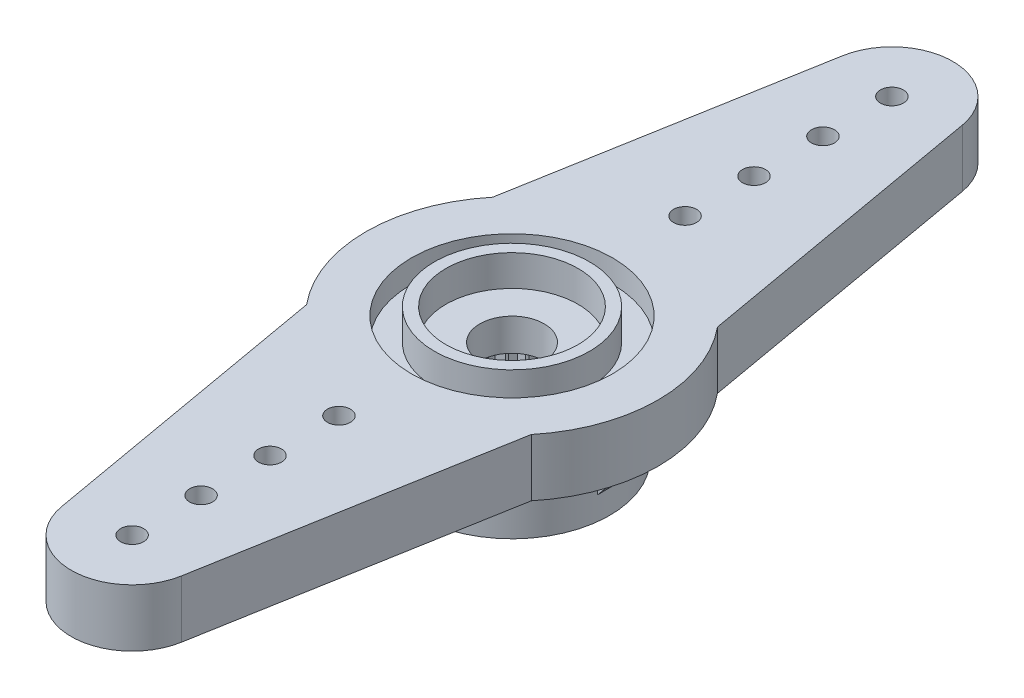
SolidWorks part; units mm, degrees
material "PC High Viscosity"
ref_plane "Front Plane" through (0, 0, 0) normal (0, 0, 1) x (1, 0, 0)
ref_plane "Top Plane" through (0, 0, 0) normal (0, 1, 0) x (1, 0, 0)
ref_plane "Right Plane" through (0, 0, 0) normal (1, 0, 0) x (0, 0, -1)
sketch "BaseS" plane through (0, 0, 0) normal (0, 1, 0) x (1, 0, 0)
  circle A0 centre (0, 0) radius 6.35
  dimension "D1" = 12.7
extrude "BASE" add sketch "BaseS" along normal blind 5.4
sketch "TopBoreS" plane through (0, 5.4, 0) normal (0, 1, 0) x (1, 0, 0)
  circle A0 centre (0, 0) radius 1.4
  dimension "D1" = 2.8
extrude "TOP BORE" cut sketch "TopBoreS" against normal through all
sketch "HornHalfS" plane through (0, 5.4, 0) normal (0, 1, 0) x (1, 0, 0)
  line L0 (0, 0) -> (0, 16.53) construction
  line L1 (-2.6097, 16.9902) -> (-4.8916, 4.049)
  line L2 (0, 19.18) -> (0, 16.53) construction
  line L3 (2.6097, 16.9902) -> (4.8916, 4.049)
  arc A0 (2.6097, 16.9902) -> (-2.6097, 16.9902) centre (0, 16.53) ccw
  arc A1 (4.8916, 4.049) -> (-4.8916, 4.049) centre (0, 0) ccw
  circle A2 centre (0, 0) radius 6.35 construction
  dimension "D1" = 5.3
  dimension "D2" = 19.18
  dimension "D3" = 10
  dimension "D4" = 9.7832
extrude "HORN HALF" add sketch "HornHalfS" against normal blind 2.5
sketch "HornAttachS" plane through (0, 5.4, 0) normal (0, 1, 0) x (1, 0, 0)
  circle A0 centre (0, 16.53) radius 0.5
  dimension "D1" = 1
extrude "HORN ATTACH" cut sketch "HornAttachS" against normal through all
sketch "HA LP RS" plane through (0, 0, 0) normal (0, 1, 0) x (1, 0, 0)
  line L0 (0, 0) -> (0, 16.53) construction
pattern_linear "HA LP" count 4 spacing 3 along (0, 0, 1) of "HORN ATTACH"
mirror "HORN BODIES" about plane through (0, 0, 0) normal (0, 0, 1) of "HA LP", "HORN ATTACH", "HORN HALF"
sketch "ToothS" plane through (0, 0, 0) normal (0, -1, 0) x (1, 0, 0)
  line L0 (0, -2.9) -> (0.2629, -2.5867)
  line L1 (0, -2.9) -> (-0.2629, -2.5867)
  line L2 (0, -2.6) -> (0, -2.9) construction
  line L3 (0, 0) -> (0, -2.6) construction
  arc A0 (-0.2629, -2.5867) -> (0.2629, -2.5867) centre (0, 0) ccw
  dimension "D1" = 5.2
  dimension "D2" = 80
  dimension "D3" = 0.3
extrude "TOOTH" cut sketch "ToothS" against normal blind 3
pattern_circular "TOOTH CP" count 26 over 360 about axis through (0, 0, 0) along (0, 1, 0) of "TOOTH"
sketch "BottomBoreS" plane through (0, 0, 0) normal (0, -1, 0) x (-1, 0, 0)
  circle A0 centre (0, 0) radius 2.6
  arc A1 (0.2629, 2.5867) -> (-0.2629, 2.5867) centre (0, 0) ccw construction
extrude "BOTTOM BORE" cut sketch "BottomBoreS" against normal up to surface (3 mm away) up to face at (-0.6451, 3, 2.6172)
sketch "HoldingShaftS" plane through (0, 0, 0) normal (0, -1, 0) x (1, 0, 0)
  circle A0 centre (0, 0) radius 6.35 construction
  circle A1 centre (0, 0) radius 6.35
  circle A2 centre (0, 0) radius 4.25
  dimension "D1" = 2.1
  dimension "D2" = 8.5
extrude "HOLDING SHAFT" cut sketch "HoldingShaftS" against normal up to surface (2.9 mm away) up to face at (0, 2.9, -13.03)
sketch "RibS" plane through (0, 0, 0) normal (0, 0, 1) x (1, 0, 0)
  line L0 (4.21, 1) -> (5.8043, 2.9)
  line L1 (5.8043, 2.9) -> (4.21, 2.9)
  line L2 (4.21, 1) -> (4.16, 1)
  line L3 (4.16, 1) -> (4.16, 2.9)
  line L4 (4.21, 1) -> (4.21, 2.9) construction
  line L5 (4.16, 2.9) -> (4.21, 2.9)
  line L6 (-4.25, 2.9) -> (4.25, 2.9) construction
  line L7 (4.21, 2.9) -> (4.25, 2.9) construction
  line L8 (4.25, 0) -> (4.25, 2.9) construction
  dimension "D1" = 1.9
  dimension "D2" = 0.05
  dimension "D3" = 40
  dimension "D4" = 0.09
extrude "RIB" add sketch "RibS" along normal mid plane 1
pattern_circular "RIB CP" count 4 over 360 about axis through (0, 0, 0) along (0, 1, 0) of "RIB"
sketch "TopCutS" plane through (0, 5.4, 0) normal (0, 1, 0) x (1, 0, 0)
  circle A0 centre (0, 0) radius 4.375
  arc A1 (4.8916, -4.049) -> (4.8916, 4.049) centre (0, 0) ccw construction
  dimension "D1" = 1.975
  dimension "D2" = 8.75
extrude "TOP CUT" cut sketch "TopCutS" against normal blind 1
sketch "TopPocketCylinderS" plane through (0, 4.4, 0) normal (0, 1, 0) x (1, 0, 0)
  circle A0 centre (0, 0) radius 2.875
  circle A1 centre (0, 0) radius 3.375
  circle A2 centre (0, 0) radius 4.375 construction
  dimension "D2" = 0.5
  dimension "D1" = 1
  dimension "D3" = 6.75
extrude "TOP POCKET CYLINDER" add sketch "TopPocketCylinderS" along normal offset from surface (1.35 mm away) 0.35 up to face at (0, 5.4, 4.375) offset beyond the face yes
